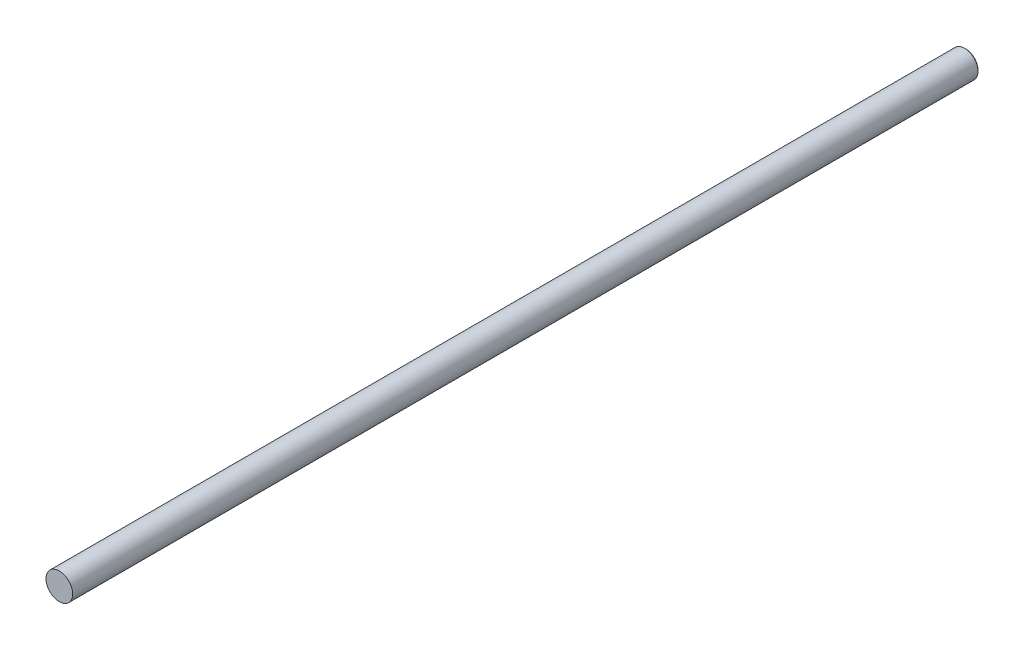
SolidWorks part; units mm, degrees
material "Alloy Steel"
ref_plane "Plane1" through (0, 0, 0) normal (0, 0, 1) x (1, 0, 0)
ref_plane "Plane2" through (0, 0, 0) normal (0, 1, 0) x (1, 0, 0)
ref_plane "Plane3" through (0, 0, 0) normal (1, 0, 0) x (0, 0, -1)
sketch "Sketch1" plane through (0, 0, 0) normal (0, 0, 1) x (1, 0, 0)
  circle A0 centre (0, 0) radius 3.175
  dimension "Diameter" = 6.35
extrude "Base-Extrude" add sketch "Sketch1" against normal blind 215.9
chamfer "Chamfer1" distance 0.254 angle 45 1 edges at (3.175, 0, -215.9)
